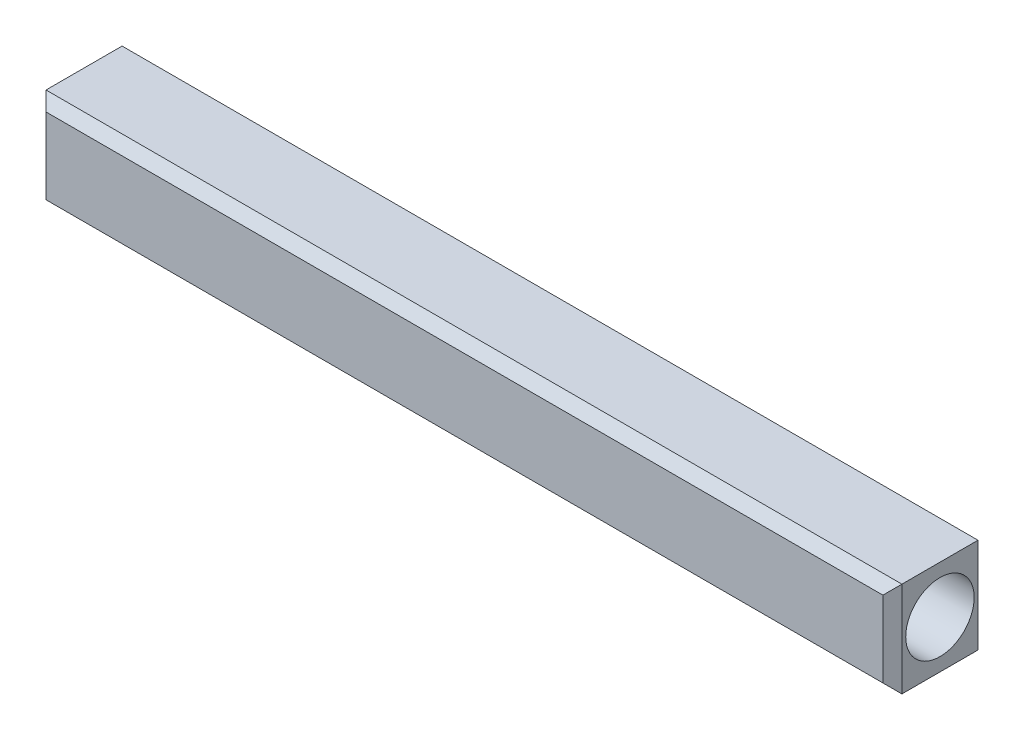
SolidWorks part; units mm, degrees
ref_plane "Front Plane" through (0, 0, 0) normal (0, 0, 1) x (1, 0, 0)
ref_plane "Top Plane" through (0, 0, 0) normal (0, 1, 0) x (1, 0, 0)
ref_plane "Right Plane" through (0, 0, 0) normal (1, 0, 0) x (0, 0, -1)
sketch "Sketch1" plane through (0, 0, 0) normal (0, 0, 1) x (1, 0, 0)
  line L0 (0, 0) -> (0, 5)
  line L3 (-22.5, 5) -> (0, 5)
  line L4 (-22.5, 0) -> (0, 0)
  line L5 (-22.5, 5) -> (-22.5, 0)
  dimension "D1" = 22.5
  dimension "D3" = 5
extrude "Boss-Extrude1" add sketch "Sketch1" along normal blind 5
sketch "Sketch2" plane through (-22.5, 0, 0) normal (-1, 0, 0) x (0, 0, 1)
  line L0 (0, 2.5) -> (5, 2.5) construction
  line L1 (0, 5) -> (0, 0) construction
  line L2 (5, 5) -> (5, 0) construction
  line L4 (0, 5) -> (0, 0) construction
  circle A0 centre (2.5, 2.5) radius 1.8
  point P10 (0, 2.5)
  dimension "D1" = 3.6
extrude "Cut-Extrude1" cut sketch "Sketch2" against normal blind 5
mirror "Mirror1" about plane through (0, 0, 0) normal (1, 0, 0) of "Cut-Extrude1", "Boss-Extrude1"
chamfer "Chamfer1" distance 0.5 angle 45 8 edges at (0, 5, 5) (-22.5, 2.5, 5) (22.5, 2.5, 5) (22.5, 2.5, 0) (0, 0, 5) (-22.5, 2.5, 0) (0, 5, 0) (0, 0, 0)
